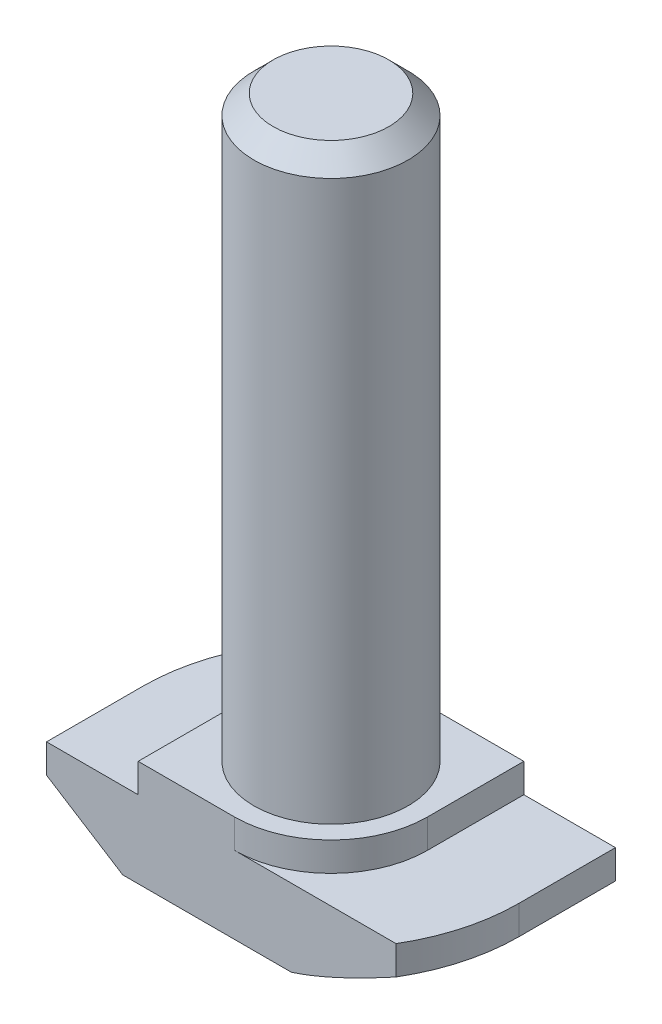
SolidWorks part; units mm, degrees
ref_plane "Спереди" through (0, 0, 0) normal (0, 0, 1) x (1, 0, 0)
ref_plane "Сверху" through (0, 0, 0) normal (0, 1, 0) x (1, 0, 0)
ref_plane "Справа" through (0, 0, 0) normal (1, 0, 0) x (0, 0, -1)
sketch "Эскиз1" plane through (0, 0, 0) normal (0, 0, 1) x (1, 0, 0)
  line L0 (9.75, 0) -> (-9.75, 0)
  line L1 (-9.75, 0) -> (-9.75, 4)
  line L2 (-9.75, 4) -> (-5, 4)
  line L3 (-5, 4) -> (-5, 5.5)
  line L4 (-5, 5.5) -> (5, 5.5)
  line L5 (0, 5.5) -> (0, 0) construction
  line L6 (5, 4) -> (5, 5.5)
  line L7 (9.75, 4) -> (5, 4)
  line L8 (9.75, 0) -> (9.75, 4)
  point P12 (-8.25, 2.6435)
  point P13 (-4, 3.6993)
  dimension "D1" = 10
  dimension "D2" = 19.5
  dimension "D3" = 5.5
  dimension "D4" = 1.5
extrude "Бобышка-Вытянуть1" add sketch "Эскиз1" along normal mid plane 10
sketch "Эскиз3" plane through (0, 5.5, 0) normal (0, 1, 0) x (1, 0, 0)
  line L1 (5, 5) -> (-5, 5) construction
  line L2 (-5, 0) -> (-5, 5)
  line L3 (-5, 5) -> (0, 5)
  line L4 (0, -5) -> (5, -5)
  line L5 (5, -5) -> (-5, -5) construction
  line L6 (5, -5) -> (5, 0)
  line L7 (5, -5) -> (5, 5) construction
  arc A0 (-5, 0) -> (0, 5) centre (0, 0) cw
  arc A1 (5, 0) -> (0, -5) centre (0, 0) cw
extrude "Вырез-Вытянуть1" cut sketch "Эскиз3" against normal up to surface (1.5 mm away) up to face at (-7.375, 4, 0)
sketch "Эскиз2" plane through (0, 5.5, 0) normal (0, 1, 0) x (1, 0, 0)
  circle A0 centre (0, 0) radius 4
  dimension "D1" = 8
extrude "Бобышка-Вытянуть2" add sketch "Эскиз2" along normal blind 30
cosmetic thread "Условное изображение резьбы1" parameters "D1"=30, "D2"=6.619
sketch "Эскиз4" plane through (0, 4, 0) normal (0, 1, 0) x (1, 0, 0)
  line L0 (-9.75, -5) -> (-9.75, 5) construction
  line L1 (9.75, -5) -> (9.75, 5) construction
  line L2 (-8.3703, 5) -> (-9.75, 5)
  line L3 (-9.75, 5) -> (-9.75, 0)
  line L4 (8.3703, -5) -> (9.75, -5)
  line L5 (9.75, -5) -> (9.75, 0)
  arc A0 (-9.75, 0) -> (-8.3703, 5) centre (0, 0) cw
  arc A1 (9.75, 0) -> (8.3703, -5) centre (0, 0) cw
extrude "Вырез-Вытянуть2" cut sketch "Эскиз4" against normal through all
sketch "Эскиз5" plane through (0, 0, 5) normal (0, 0, 1) x (1, 0, 0)
  line L0 (-9.75, 2.5) -> (-5.8, 0)
  line L1 (-9.75, 4) -> (-9.75, 0) construction
  line L2 (-9.75, 0) -> (8.3703, 0) construction
  line L3 (-5.8, 0) -> (-9.75, 0)
  line L4 (-9.75, 0) -> (-9.75, 2.5)
  line L6 (-5, 4) -> (-9.75, 4) construction
  line L7 (-5, 5.5) -> (-5, 4) construction
  point P6 (-4.9519, 0)
  point P9 (0, 0)
  point P10 (-4.6154, 0)
  point P12 (-8.25, 2.2665)
  point P15 (0, 0)
  dimension "D1" = 1.5
  dimension "D2" = 0.8
sketch "Эскиз6" plane through (0, 0, 0) normal (0, -1, 0) x (1, 0, 0)
  line L0 (0, -9.75) -> (9.75, -9.75)
  line L1 (9.75, -9.75) -> (9.75, 0)
  line L2 (0, 9.75) -> (-9.75, 9.75)
  line L3 (-9.75, 9.75) -> (-9.75, 0)
  arc A0 (-9.75, 0) -> (0, -9.75) centre (0, 0) ccw
  arc A1 (9.75, 0) -> (0, 9.75) centre (0, 0) ccw
  point P10 (0, 0)
sweep "Вырез-По траектории1" cut profiles "Эскиз5" path "Эскиз6"
chamfer "Фаска2" distance 1 angle 45 1 edges at (0, 35.5, 4)
